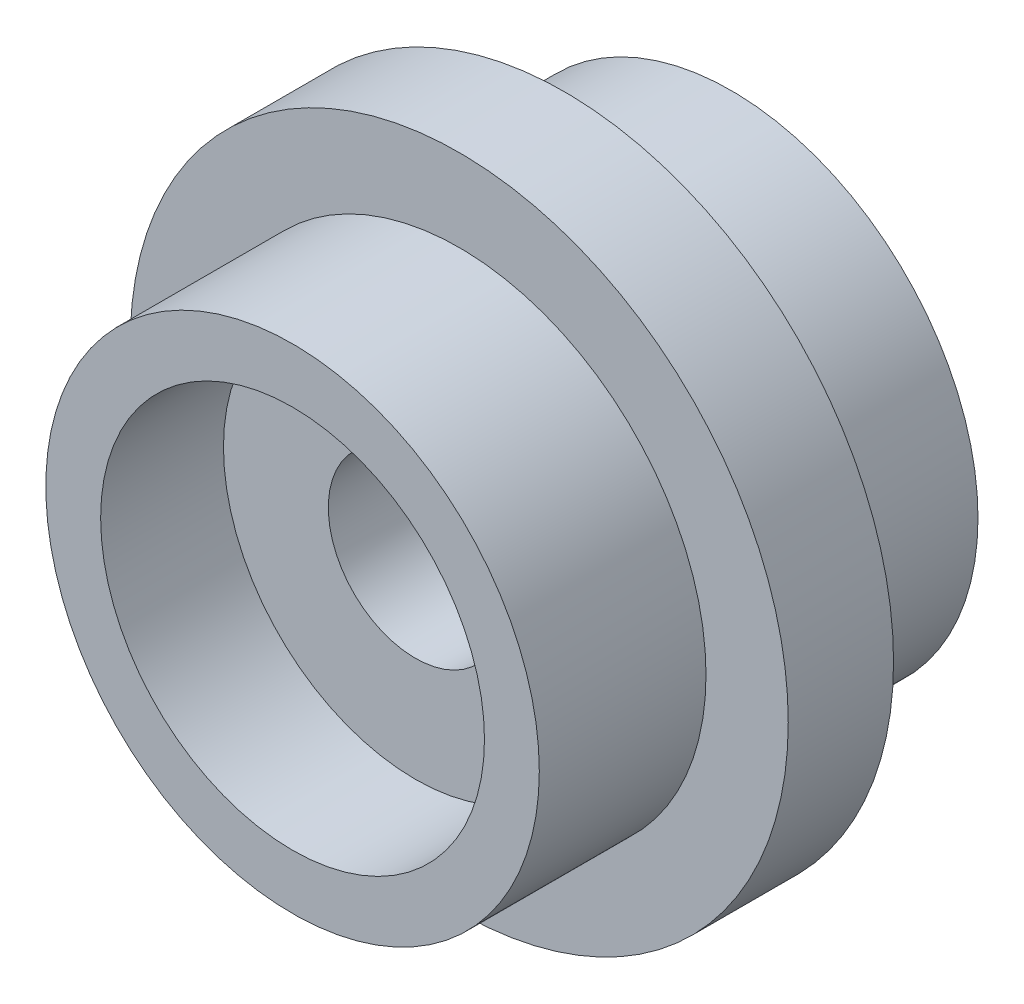
SolidWorks part; units mm, degrees
ref_plane "Front Plane" through (0, 0, 0) normal (0, 0, 1) x (1, 0, 0)
ref_plane "Top Plane" through (0, 0, 0) normal (0, 1, 0) x (1, 0, 0)
ref_plane "Right Plane" through (0, 0, 0) normal (1, 0, 0) x (0, 0, -1)
sketch "Sketch1" plane through (0, 0, 0) normal (1, 0, 0) x (0, 0, -1)
  line L0 (-13.6967, 0) -> (33.3737, 0) construction
  line L1 (0, 0) -> (0, 14.2875)
  line L2 (0, 14.2875) -> (9.652, 14.2875)
  line L3 (25.4, 14.2875) -> (25.4, 0)
  line L4 (25.4, 0) -> (0, 0)
  line L5 (9.652, 14.2875) -> (9.652, 19.05)
  line L6 (9.652, 19.05) -> (15.748, 19.05)
  line L7 (15.748, 19.05) -> (15.748, 14.2875)
  line L8 (15.748, 14.2875) -> (25.4, 14.2875)
  point P9 (12.7, 0)
  point P12 (12.7, 19.05)
  dimension "D1" = 14.2875
  dimension "D2" = 25.4
  dimension "D3" = 6.096
  dimension "D4" = 19.05
revolve "Revolve1" add sketch "Sketch1" angle 360 about L0
hole_wizard "3/8 Clearance Hole1" positions "Sketch2" profile "Sketch3" hole size "3/8" standard "ANSI Inch" end condition up to next
sketch "Sketch2" plane through (0, 0, 0) normal (0, 0, 1) x (1, 0, 0)
  point P0 (0, 0)
sketch "Sketch3" plane through (0, 0, 0) normal (1, 0, 0) x (0, -1, 0)
  line L0 (0, 0) -> (0, 25.4)
  line L1 (0, 25.4) -> (5.0419, 25.4)
  line L2 (5.0419, 25.4) -> (5.0419, 0)
  line L5 (5.0419, 0) -> (0, 0)
  line L11 (0, -6.35) -> (0, 107.95) construction
  dimension "Thru Hole Dia." = 10.0838
  dimension "Thru Hole Depth" = 25.4
sketch "Sketch6" plane through (0, 0, 0) normal (0, 0, 1) x (1, 0, 0)
  circle A0 centre (0, 0) radius 11.1125
  dimension "D1" = 22.225
extrude "Cut-Extrude1" cut sketch "Sketch6" against normal blind 7.112
sketch "Sketch7" plane through (0, 0, -25.4) normal (0, 0, -1) x (-1, 0, 0)
  circle A0 centre (0, 0) radius 11.1125
  dimension "D1" = 22.225
extrude "Cut-Extrude2" cut sketch "Sketch7" against normal blind 12.065
ref_plane "Plane1" through (0, 0, -12.7) normal (0, 0, 1) x (1, 0, 0)
